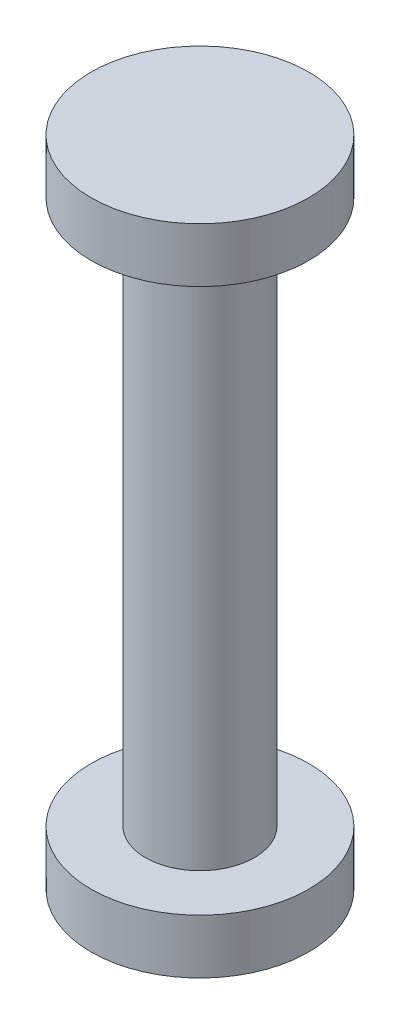
SolidWorks part; units mm, degrees
ref_plane "Front Plane" through (0, 0, 0) normal (0, 0, 1) x (1, 0, 0)
ref_plane "Top Plane" through (0, 0, 0) normal (0, 1, 0) x (1, 0, 0)
ref_plane "Right Plane" through (0, 0, 0) normal (1, 0, 0) x (0, 0, -1)
sketch "Sketch1" plane through (0, 0, 0) normal (0, 1, 0) x (1, 0, 0)
  circle A0 centre (0, 0) radius 5
  dimension "D1" = 10
extrude "Boss-Extrude1" add sketch "Sketch1" along normal blind 50 from offset 25 offset against normal yes
sketch "Sketch2" plane through (0, 25, 0) normal (0, 1, 0) x (1, 0, 0)
  circle A0 centre (0, 0) radius 10
  dimension "D1" = 20
extrude "Boss-Extrude2" add sketch "Sketch2" along normal blind 5 contours A0
mirror "Mirror1" about plane through (0, 0, 0) normal (0, 1, 0) of "Boss-Extrude2"
